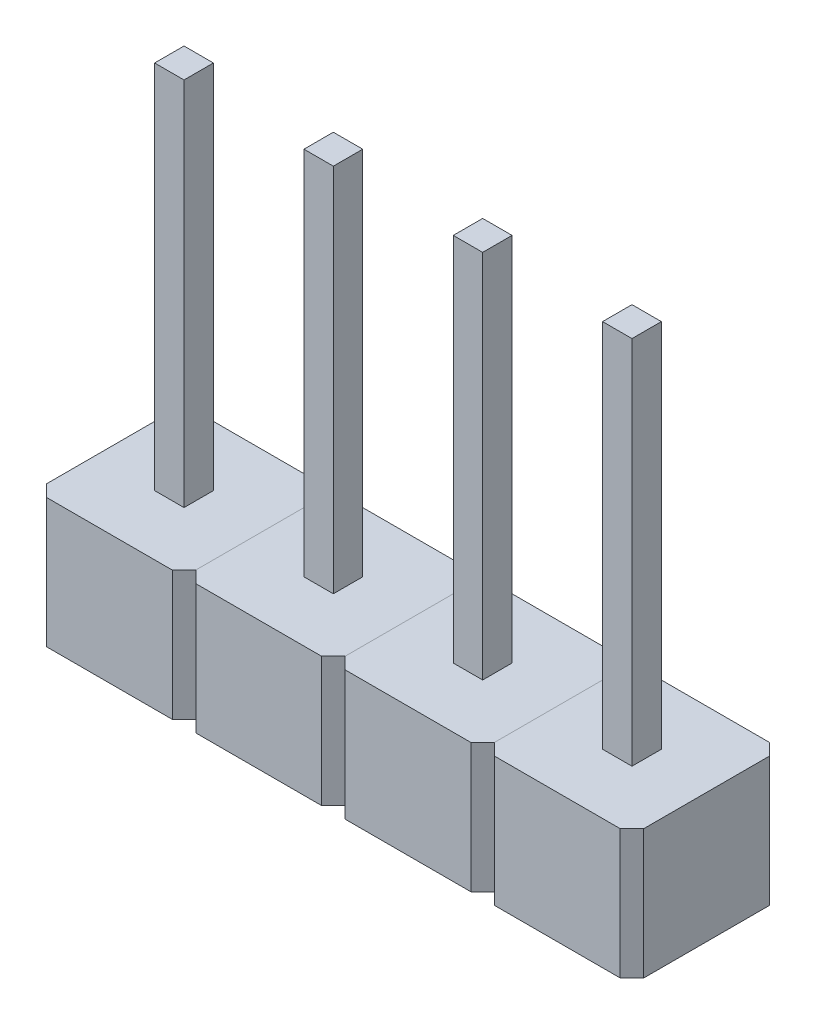
SolidWorks part; units mm, degrees
ref_plane "Alzado" through (0, 0, 0) normal (0, 0, 1) x (1, 0, 0)
ref_plane "Planta" through (0, 0, 0) normal (0, 1, 0) x (1, 0, 0)
ref_plane "Vista lateral" through (0, 0, 0) normal (1, 0, 0) x (0, 0, -1)
sketch "Croquis1" plane through (0, 0, 0) normal (0, 1, 0) x (1, 0, 0)
  line L0 (2.54, 0) -> (3.04, 0)
  line L1 (0, 0) -> (0.5, 0)
  line L2 (0, 0) -> (0, 0.5)
  line L3 (0, 0.5) -> (0.5, 0.5)
  line L4 (0.5, 0) -> (0.5, 0.5)
  line L5 (2.54, 0) -> (2.54, 0.5)
  line L6 (2.54, 0.5) -> (3.04, 0.5)
  line L7 (3.04, 0) -> (3.04, 0.5)
  line L8 (5.08, 0) -> (5.58, 0)
  line L9 (5.08, 0) -> (5.08, 0.5)
  line L10 (5.08, 0.5) -> (5.58, 0.5)
  line L11 (5.58, 0) -> (5.58, 0.5)
  line L12 (7.62, 0) -> (8.12, 0)
  line L13 (7.62, 0) -> (7.62, 0.5)
  line L14 (7.62, 0.5) -> (8.12, 0.5)
  line L15 (8.12, 0) -> (8.12, 0.5)
  dimension "D1" = 0.5
  dimension "D2" = 0.5
extrude "Extruir1" add sketch "Croquis1" along normal blind 8.5
sketch "Croquis2" plane through (0, 0, 0) normal (0, -1, 0) x (1, 0, 0)
  line L0 (0, 0) -> (0.5, 0) construction
  line L1 (-1.02, 1.02) -> (1.52, 1.02)
  line L2 (-1.02, 1.02) -> (-1.02, -1.52)
  line L3 (-1.02, -1.52) -> (1.52, -1.52)
  line L4 (1.52, 1.02) -> (1.52, -1.52)
  line L5 (0, -0.5) -> (0, 0) construction
  line L7 (0, 0) -> (0.5, 0)
  line L8 (0, 0) -> (0, -0.5)
  line L9 (0, -0.5) -> (0.5, -0.5)
  line L10 (0.5, 0) -> (0.5, -0.5)
  point P4 (0.25, 0)
  point P7 (0, -0.25)
  dimension "D1" = 2.54
  dimension "D2" = 2.54
  dimension "D3" = 1.27
  dimension "D4" = 1.27
extrude "Extruir2" add sketch "Croquis2" against normal blind 2.2 separate body
chamfer "Chaflán1" distance 0.2 angle 45 4 edges at (1.52, 1.1, -1.52) (1.52, 1.1, 1.02) (-1.02, 1.1, -1.52) (-1.02, 1.1, 1.02)
pattern_linear "MatrizL1" count 4 spacing 2.54 along (1, 0, 0) of bodies 106
